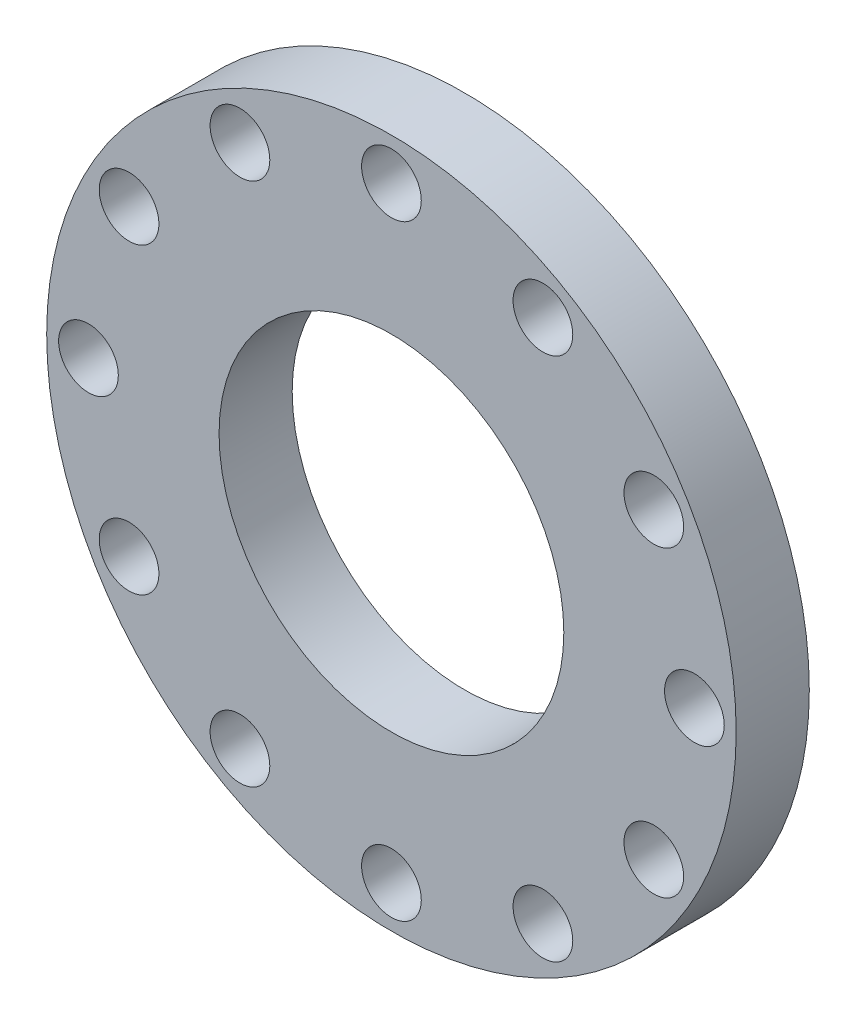
SolidWorks part; units mm, degrees
ref_plane "Front Plane" through (0, 0, 0) normal (0, 0, 1) x (1, 0, 0)
ref_plane "Top Plane" through (0, 0, 0) normal (0, 1, 0) x (1, 0, 0)
ref_plane "Right Plane" through (0, 0, 0) normal (1, 0, 0) x (0, 0, -1)
sketch "Sketch1" plane through (0, 0, 0) normal (0, 0, 1) x (1, 0, 0)
  circle A0 centre (0, 0) radius 330
  circle A1 centre (0, 0) radius 165
  dimension "D1" = 660
  dimension "D2" = 330
extrude "Boss-Extrude1" add sketch "Sketch1" along normal blind 70
sketch "Sketch2" plane through (0, 0, 0) normal (0, 0, 1) x (1, 0, 0)
  circle A0 centre (0, 0) radius 290
  circle A1 centre (0, 290) radius 28.575
  circle A2 centre (145, 251.1474) radius 28.575
  circle A3 centre (251.1474, 145) radius 28.575
  circle A4 centre (290, 0) radius 28.575
  circle A5 centre (251.1474, -145) radius 28.575
  circle A6 centre (145, -251.1474) radius 28.575
  circle A7 centre (0, -290) radius 28.575
  circle A8 centre (-145, -251.1474) radius 28.575
  circle A9 centre (-251.1474, -145) radius 28.575
  circle A10 centre (-290, 0) radius 28.575
  circle A11 centre (-251.1474, 145) radius 28.575
  circle A12 centre (-145, 251.1474) radius 28.575
  point P30 (0, 0)
  dimension "D1" = 580
  dimension "D2" = 57.15
  dimension "D3" = 12
extrude "Cut-Extrude1" cut sketch "Sketch2" along normal blind 131 contours A0 A4 | A0 A4 | A0 A6 | A0 A8 | A0 A8 | A5 | A7 | A9 | A10 | A11 | A12 | A1 | A2 | A3
equation "\"2.25inch\"=0.0379964"
